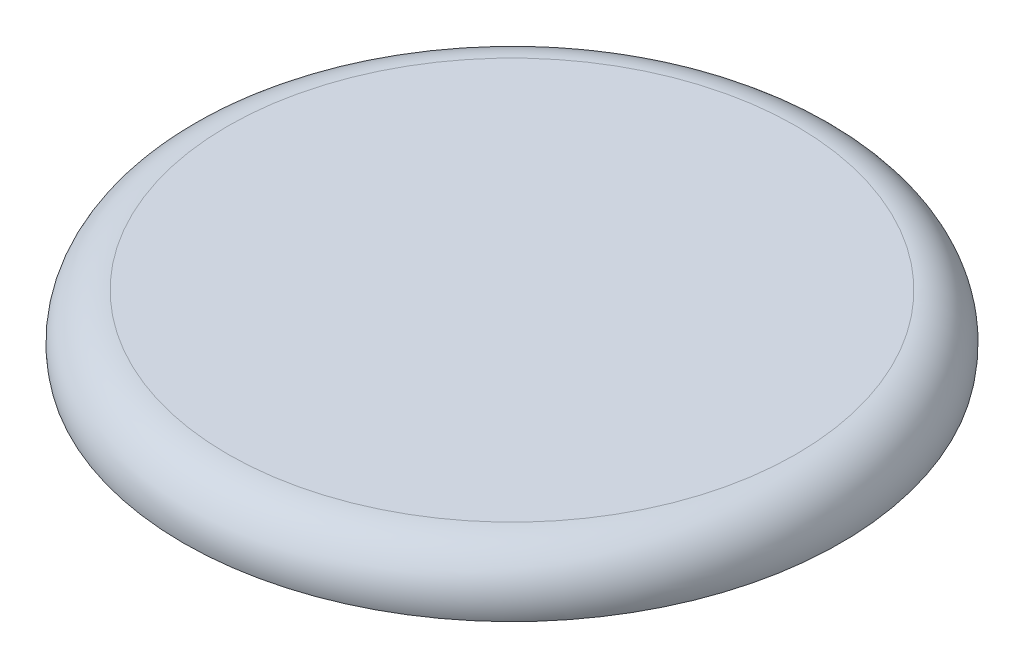
SolidWorks part; units mm, degrees
material "PLA"
ref_plane "Front Plane" through (0, 0, 0) normal (0, 0, 1) x (1, 0, 0)
ref_plane "Top Plane" through (0, 0, 0) normal (0, 1, 0) x (1, 0, 0)
ref_plane "Right Plane" through (0, 0, 0) normal (1, 0, 0) x (0, 0, -1)
sketch "Sketch1" plane through (0, 0, 0) normal (0, 1, 0) x (1, 0, 0)
  circle A0 centre (0, 0) radius 75
  dimension "D1" = 150
extrude "Boss-Extrude1" add sketch "Sketch1" against normal blind 100 draft 12
ref_plane "Plane1" through (0, -10, 0) normal (0, 1, 0) x (1, 0, 0)
sketch "Sketch3" plane through (0, -10, 0) normal (0, 1, 0) x (1, 0, 0)
  circle A0 centre (0, 0) radius 70
  dimension "D1" = 140
extrude "Cut-Extrude1" cut sketch "Sketch3" against normal blind 80 draft 12
fillet "Fillet1" radius 10 1 edges at (0, 0, 75)
sketch "Sketch4" plane through (0, 0, 0) normal (0, 0, 1) x (1, 0, 0)
  line L0 (-15, -70) -> (15, -70)
  circle A0 centre (-25, -40) radius 15
  circle A1 centre (25, -40) radius 15
  arc A2 (-15, -70) -> (15, -70) centre (0, -70) ccw
  dimension "D1" = 30
  dimension "D2" = 50
  dimension "D3" = 25
  dimension "D4" = 40
  dimension "D5" = 30
  dimension "D6" = 70
extrude "Cut-Extrude2" cut sketch "Sketch4" against normal blind 90
sketch "Sketch5" plane through (0, -100, 0) normal (0, -1, 0) x (1, 0, 0)
  circle A0 centre (0, 0) radius 14.5
  circle A1 centre (0, 0) radius 12.5
  dimension "D1" = 29
  dimension "D2" = 25
extrude "Boss-Extrude2" add sketch "Sketch5" along normal blind 30
sketch "Sketch6" plane through (0, -100, 0) normal (0, -1, 0) x (1, 0, 0)
  circle A1 centre (0, 0) radius 12.5
  circle A2 centre (0, 0) radius 12.5
  dimension "D1" = 0
extrude "Cut-Extrude3" cut sketch "Sketch6" against normal blind 30
ref_plane "Plane2" through (0, -12.0791, 0) normal (0, 1, 0) x (1, 0, 0)
sketch "Sketch7" plane through (0, -12.0791, 0) normal (0, 1, 0) x (1, 0, 0)
  circle A0 centre (0, 0) radius 73.5
  dimension "D1" = 147
extrude "Cut-Extrude4" cut sketch "Sketch7" against normal blind 130
